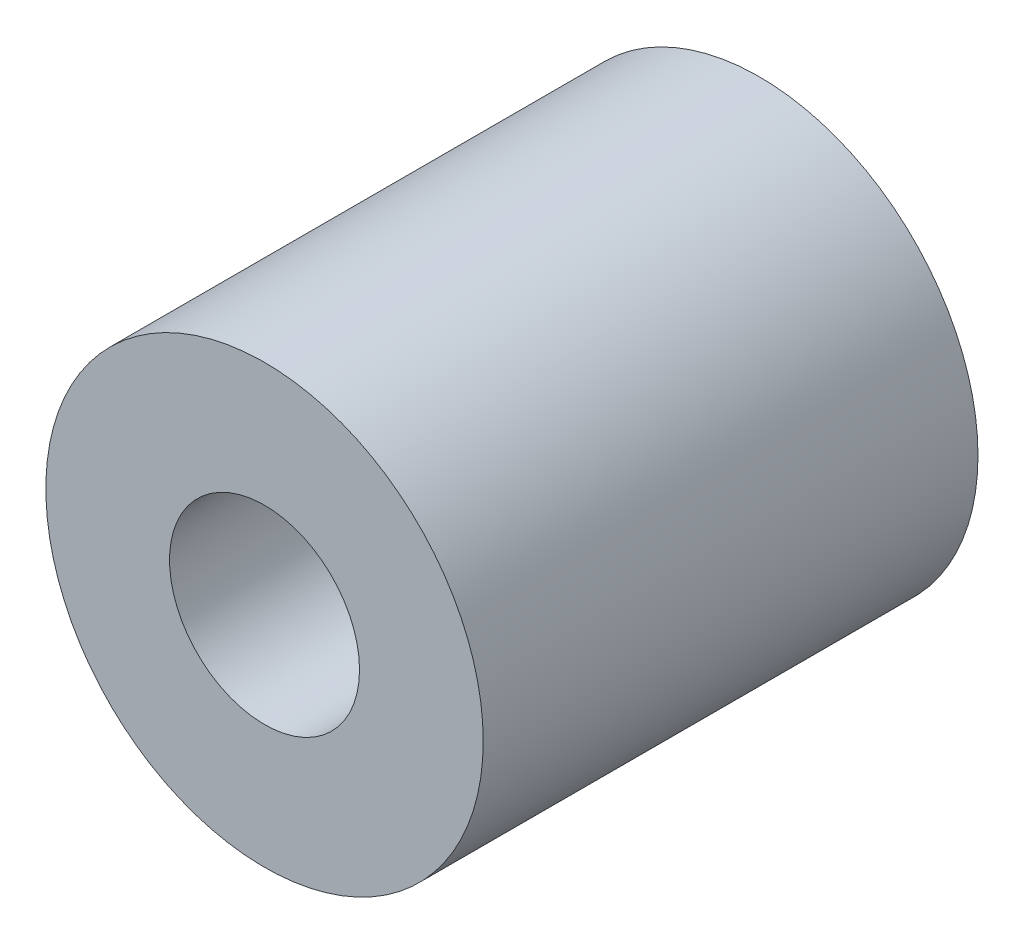
SolidWorks part; units mm, degrees
material "PPE"
ref_plane "Front Plane" through (0, 0, 0) normal (0, 0, 1) x (1, 0, 0)
ref_plane "Top Plane" through (0, 0, 0) normal (0, 1, 0) x (1, 0, 0)
ref_plane "Right Plane" through (0, 0, 0) normal (1, 0, 0) x (0, 0, -1)
sketch "Sketch1" plane through (0, 0, 0) normal (0, 0, 1) x (1, 0, 0)
  circle A0 centre (0, 0) radius 5.6134
  circle A1 centre (0, 0) radius 2.4384
  dimension "D1" = 11.2268
  dimension "D2" = 4.8768
extrude "Boss-Extrude1" add sketch "Sketch1" along normal blind 12.7
